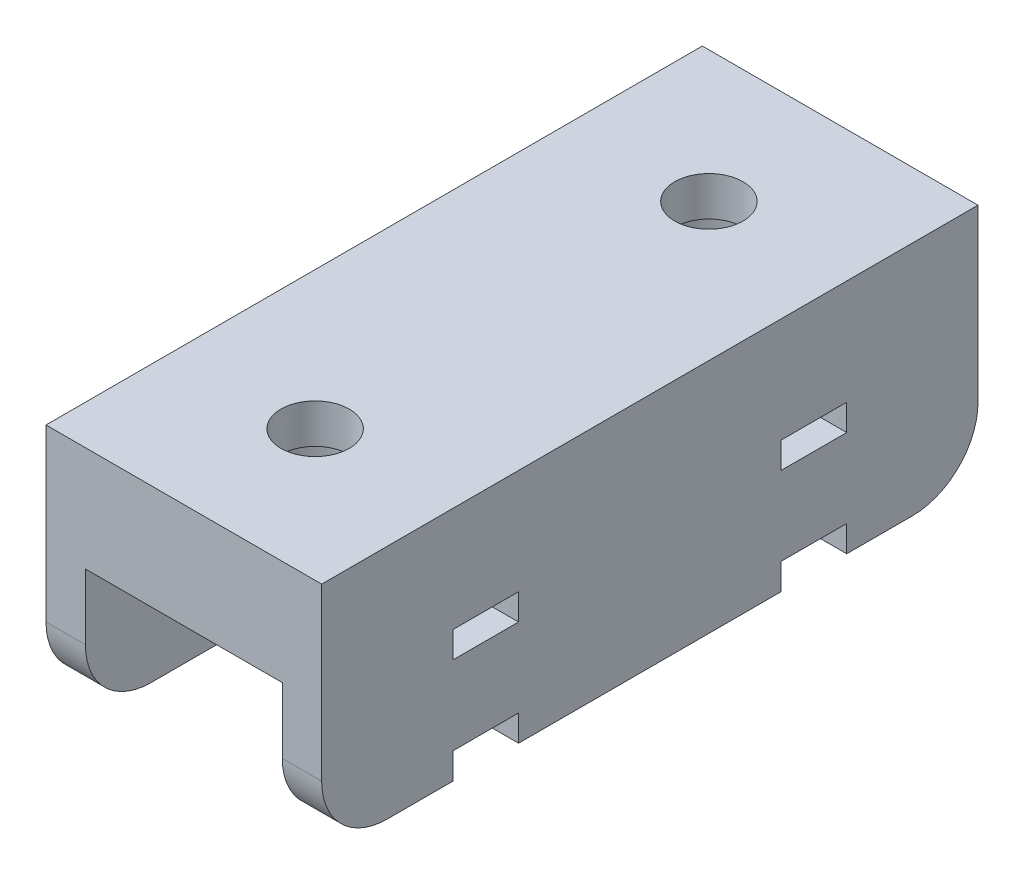
SolidWorks part; units mm, degrees
ref_plane "Front Plane" through (0, 0, 0) normal (0, 0, 1) x (1, 0, 0)
ref_plane "Top Plane" through (0, 0, 0) normal (0, 1, 0) x (1, 0, 0)
ref_plane "Right Plane" through (0, 0, 0) normal (1, 0, 0) x (0, 0, -1)
sketch "Sketch1" plane through (0, 0, 0) normal (0, 1, 0) x (1, 0, 0)
  line L0 (0, 25) -> (0, -25) construction
  line L1 (-10.5, 25) -> (10.5, 25)
  line L2 (-10.5, 25) -> (-10.5, -25)
  line L3 (-10.5, -25) -> (10.5, -25)
  line L4 (10.5, 25) -> (10.5, -25)
  line L5 (-10.5, 25) -> (10.5, -25) construction
  line L6 (-10.5, -25) -> (10.5, 25) construction
  line L7 (-10.5, 0) -> (10.5, 0) construction
  circle A0 centre (0, -15) radius 2.6
  circle A3 centre (0, 15) radius 2.6
  point P0 (0, 0)
  dimension "D4" = 5.2
  dimension "D1" = 21
  dimension "D2" = 50
  dimension "D3" = 10
extrude "Boss-Extrude1" add sketch "Sketch1" along normal blind 8
sketch "Sketch2" plane through (0, 0, 0) normal (0, -1, 0) x (1, 0, 0)
  circle A1 centre (0, 15) radius 4.5
  circle A2 centre (0, -15) radius 4.5
extrude "Cut-Extrude1" cut sketch "Sketch2" against normal blind 5
sketch "Sketch3" plane through (0, 0, 25) normal (0, 0, 1) x (1, 0, 0)
  line L14 (0, 0) -> (0, -10) construction
  line L23 (-10.5, 0) -> (10.5, 0)
  line L24 (-10.5, 0) -> (-10.5, -10)
  line L25 (-10.5, -10) -> (10.5, -10)
  line L26 (10.5, 0) -> (10.5, -10)
  line L27 (-10.5, 0) -> (-7.5, 0)
  line L28 (-10.5, 0) -> (-10.5, -10)
  line L29 (-10.5, -10) -> (-7.5, -10)
  line L30 (-7.5, 0) -> (-7.5, -10)
  line L31 (10.5, -10) -> (7.5, -10)
  line L32 (7.5, 0) -> (7.5, -10)
  line L33 (10.5, 0) -> (7.5, 0)
  line L34 (10.5, 0) -> (10.5, -10)
  point P11 (-7.5, -5)
  dimension "D1" = 10
  dimension "D2" = 3
extrude "Boss-Extrude2" add sketch "Sketch3" against normal up to surface (50 mm away) up to face at (0, 4, -25)
sketch "Sketch4" plane through (10.5, 13.5, 0) normal (1, 0, 0) x (0, -1, 0)
  line L0 (23.5, 25) -> (13.5, 25) construction
  line L3 (23.5, 25) -> (13.5, 25)
  line L6 (23.5, 25) -> (23.5, -25)
  line L40 (23.5, -25) -> (13.5, -25)
  line L41 (13.5, 25) -> (13.5, -25)
  line L42 (5.5, -25) -> (5.5, 25) construction
  line L43 (13.5, 0) -> (23.5, 0) construction
  line L44 (18.5, -25) -> (18.5, 25) construction
  line L45 (13.5, -15) -> (15.5, -15)
  line L46 (13.5, -15) -> (13.5, -10)
  line L47 (13.5, -10) -> (15.5, -10)
  line L48 (15.5, -15) -> (15.5, -10)
  line L49 (13.5, 10) -> (15.5, 10)
  line L50 (15.5, 15) -> (15.5, 10)
  line L51 (13.5, 15) -> (15.5, 15)
  line L52 (13.5, 15) -> (13.5, 10)
  line L53 (23.5, 15) -> (23.5, 10)
  line L54 (23.5, 15) -> (21.5, 15)
  line L55 (21.5, 15) -> (21.5, 10)
  line L56 (23.5, 10) -> (21.5, 10)
  line L57 (23.5, -10) -> (21.5, -10)
  line L58 (21.5, -15) -> (21.5, -10)
  line L59 (23.5, -15) -> (21.5, -15)
  line L60 (23.5, -15) -> (23.5, -10)
  point P14 (15.5, -12.5)
  dimension "D1" = 2
  dimension "D2" = 5
  dimension "D3" = 12.5
extrude "Cut-Extrude2" cut sketch "Sketch4" against normal through all contours L45 L48 L47 L41 | L59 L6 L57 L58 | L56 L6 L54 L55 | L51 L41 L49 L50
fillet "Fillet1" radius 5 4 edges at (-9, -10, -25) (-9, -10, 25) (9, -10, 25) (9, -10, -25)
